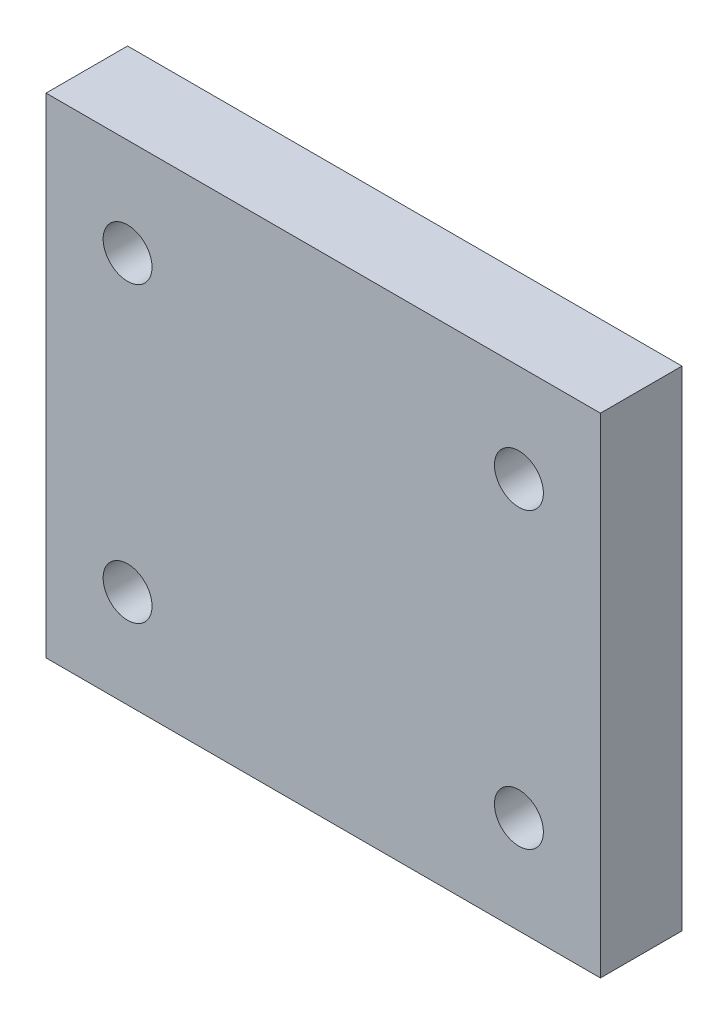
SolidWorks part; units mm, degrees
ref_plane "Front Plane" through (0, 0, 0) normal (0, 0, 1) x (1, 0, 0)
ref_plane "Top Plane" through (0, 0, 0) normal (0, 1, 0) x (1, 0, 0)
ref_plane "Right Plane" through (0, 0, 0) normal (1, 0, 0) x (0, 0, -1)
sketch "Sketch1" plane through (0, 0, 0) normal (0, 0, 1) x (1, 0, 0)
  line L1 (17, -15) -> (-17, -15)
  line L2 (17, -15) -> (17, 15)
  line L3 (17, 15) -> (-17, 15)
  line L4 (-17, -15) -> (-17, 15)
  line L5 (17, -15) -> (-17, 15) construction
  line L6 (17, 15) -> (-17, -15) construction
  point P0 (0, 0)
extrude "Boss-Extrude1" add sketch "Sketch1" along normal blind 5
sketch "Sketch2" plane through (0, 0, 0) normal (0, 0, -1) x (-1, 0, 0)
  circle A1 centre (12, 9) radius 1.5
  circle A2 centre (12, 9) radius 1.5
  circle A3 centre (-12, 9) radius 1.5
  circle A4 centre (-12, 9) radius 1.5
  circle A5 centre (12, -9) radius 1.5
  circle A6 centre (12, -9) radius 1.5
  circle A7 centre (-12, -9) radius 1.5
  circle A8 centre (-12, -9) radius 1.5
  dimension "D1" = 0
  dimension "D2" = 0
  dimension "D3" = 0
  dimension "D4" = 0
extrude "Cut-Extrude1" cut sketch "Sketch2" against normal through all
